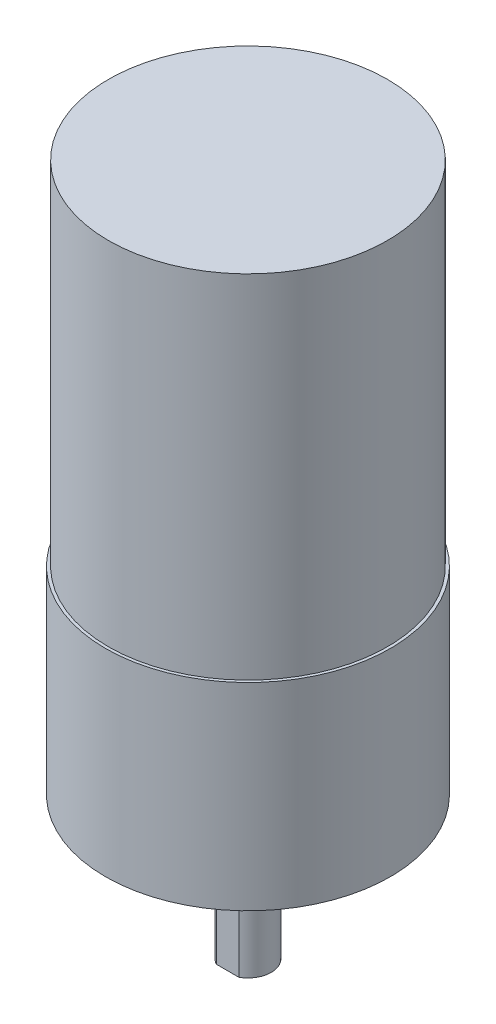
SolidWorks part; units mm, degrees
ref_plane "Front Plane" through (0, 0, 0) normal (0, 0, 1) x (1, 0, 0)
ref_plane "Top Plane" through (0, 0, 0) normal (0, 1, 0) x (1, 0, 0)
ref_plane "Right Plane" through (0, 0, 0) normal (1, 0, 0) x (0, 0, -1)
sketch "Sketch1" plane through (0, 0, 0) normal (0, 1, 0) x (1, 0, 0)
  line L0 (0, 12.446) -> (0, -12.446) construction
  line L1 (-12.446, 0) -> (12.446, 0) construction
  line L2 (-12.446, 0) -> (-9.017, 0) construction
  line L3 (9.017, 0) -> (12.446, 0) construction
  circle A0 centre (0, 0) radius 12.446
  circle A1 centre (-9.017, 0) radius 1.27
  circle A2 centre (9.017, 0) radius 1.27
  dimension "D1" = 24.892
  dimension "D3" = 2.54
  dimension "D4" = 2.54
  dimension "D2" = 18.034
extrude "Boss-Extrude1" add sketch "Sketch1" along normal blind 17.272
sketch "Sketch2" plane through (0, 17.272, 0) normal (0, 1, 0) x (1, 0, 0)
  line L0 (0, 12.446) -> (0, -12.446) construction
  line L1 (-12.446, 0) -> (12.446, 0) construction
  circle A0 centre (0, 0) radius 12.446 construction
hole_wizard "CSK for M3 Flat Head Machine Screw1" positions "Sketch3" profile "Sketch4" countersink size "M3" standard "ANSI Metric" end condition through all
sketch "Sketch3" plane through (0, 17.272, 0) normal (0, 1, 0) x (1, 0, 0)
  line L0 (0, 12.446) -> (0, -12.446) construction
  point P1 (0, 8.1199)
  point P5 (0, -7.587)
sketch "Sketch4" plane through (0, 17.272, -8.1199) normal (1, 0, 0) x (0, 0, 1)
  line L0 (0, 0) -> (0, 17.272)
  line L1 (0, 17.272) -> (1.7, 17.272)
  line L2 (1.7, 17.272) -> (1.7, 1.45)
  line L3 (1.7, 1.45) -> (3.15, 0)
  line L5 (3.15, 0) -> (0, 0)
  line L6 (-1.7, 1.45) -> (-3.15, 0) construction
  line L11 (0, -6.35) -> (0, 107.95) construction
  dimension "Thru Hole Dia." = 3.4
  dimension "Thru Hole Depth" = 17.272
  dimension "Near C'Sink Dia." = 6.3
  dimension "Near C'Sink Angle" = 90
ref_plane "Plane1" through (0, 17.272, 0) normal (0, 1, 0) x (1, 0, 0)
sketch "Sketch5" plane through (0, 17.272, 0) normal (0, 1, 0) x (1, 0, 0)
  circle A0 centre (0, 0) radius 12.192
  dimension "D1" = 24.384
extrude "Boss-Extrude2" add sketch "Sketch5" along normal blind 30.734
sketch "Sketch6" plane through (0, 0, 0) normal (0, 1, 0) x (1, 0, 0)
  circle A0 centre (0, 0) radius 3.556
  dimension "D1" = 7.112
extrude "Boss-Extrude3" add sketch "Sketch6" against normal blind 2.54
ref_plane "Plane2" through (0, -2.54, 0) normal (0, -1, 0) x (-1, 0, 0)
sketch "Sketch7" plane through (0, -2.54, 0) normal (0, -1, 0) x (-1, 0, 0)
  circle A0 centre (0, 0) radius 2.032
  dimension "D1" = 4.064
extrude "Boss-Extrude4" add sketch "Sketch7" along normal blind 9.906
ref_plane "Plane3" through (0, -12.446, 0) normal (0, -1, 0) x (-1, 0, 0)
sketch "Sketch8" plane through (0, -12.446, 0) normal (0, -1, 0) x (-1, 0, 0)
  line L0 (0, 12.446) -> (0, -12.446) construction
  line L1 (-1.016, -1.778) -> (1.016, -1.778)
  line L2 (-1.016, -1.778) -> (-1.016, -2.032)
  line L3 (-1.016, -2.032) -> (1.016, -2.032)
  line L4 (1.016, -1.778) -> (1.016, -2.032)
  line L5 (-1.016, -1.778) -> (1.016, -2.032) construction
  line L6 (-1.016, -2.032) -> (1.016, -1.778) construction
  line L7 (12.446, 0) -> (-12.446, 0) construction
  line L8 (-2.032, 0) -> (2.032, 0) construction
  line L9 (-1.016, 2.032) -> (1.016, 2.032)
  line L10 (1.016, 1.778) -> (1.016, 2.032)
  line L11 (-1.016, 1.778) -> (1.016, 1.778)
  line L12 (-1.016, 1.778) -> (-1.016, 2.032)
  circle A0 centre (0, 0) radius 2.032 construction
  point P0 (0, -1.905)
  dimension "D1" = 0.254
  dimension "D2" = 1.778
  dimension "D3" = 2.032
extrude "Cut-Extrude2" cut sketch "Sketch8" against normal blind 9.906
ref_plane "Plane4" [suppressed] through (0, 55.626, 0) normal (0, 1, 0) x (1, 0, 0)
sketch "Sketch9" [suppressed] plane through (0, 55.626, 0) normal (0, 1, 0) x (1, 0, 0)
  circle A0 centre (0, 0) radius 3.175
  dimension "D1" = 6.35
extrude "Boss-Extrude5" [suppressed] add sketch "Sketch9" along normal blind 1.524
sketch "Sketch10" [suppressed] plane through (0, 55.626, 0) normal (0, 1, 0) x (1, 0, 0)
  line L0 (0, 12.446) -> (0, -12.446) construction
  line L1 (-12.446, 0) -> (12.446, 0) construction
  line L2 (-10.033, -0.127) -> (-8.001, -0.127)
  line L3 (-10.033, -0.127) -> (-10.033, 0.127)
  line L4 (-10.033, 0.127) -> (-8.001, 0.127)
  line L5 (-8.001, -0.127) -> (-8.001, 0.127)
  line L6 (-10.033, -0.127) -> (-8.001, 0.127) construction
  line L7 (-10.033, 0.127) -> (-8.001, -0.127) construction
  line L8 (-12.192, 0) -> (-10.033, 0) construction
  line L9 (10.033, -0.127) -> (8.001, -0.127)
  line L10 (10.033, -0.127) -> (10.033, 0.127)
  line L11 (10.033, 0.127) -> (8.001, 0.127)
  line L12 (8.001, -0.127) -> (8.001, 0.127)
  line L13 (10.033, -0.127) -> (8.001, 0.127) construction
  line L14 (10.033, 0.127) -> (8.001, -0.127) construction
  line L15 (10.033, 0) -> (12.192, 0) construction
  circle A0 centre (0, 0) radius 12.192 construction
  point P4 (-9.017, 0)
  point P11 (9.017, 0)
  dimension "D1" = 18.034
  dimension "D2" = 2.032
  dimension "D3" = 0.254
  dimension "D4" = 2.032
  dimension "D5" = 0.254
extrude "Boss-Extrude6" [suppressed] add sketch "Sketch10" along normal blind 4.318
ref_plane "Plane5" [suppressed] through (0, 57.15, 0) normal (0, 1, 0) x (1, 0, 0)
sketch "Sketch11" [suppressed] plane through (0, 57.15, 0) normal (0, 1, 0) x (1, 0, 0)
  line L1 (-10.033, -0.127) -> (-8.001, -0.127)
  line L2 (-10.033, -0.127) -> (-10.033, 0.127)
  line L3 (-10.033, 0.127) -> (-8.001, 0.127)
  line L4 (-8.001, -0.127) -> (-8.001, 0.127)
  line L5 (8.001, -0.127) -> (10.033, -0.127)
  line L6 (8.001, -0.127) -> (8.001, 0.127)
  line L7 (8.001, 0.127) -> (10.033, 0.127)
  line L8 (10.033, -0.127) -> (10.033, 0.127)
  circle A0 centre (0, 0) radius 11.557
  dimension "D1" = 23.114
extrude "Boss-Extrude7" [suppressed] add sketch "Sketch11" along normal blind 0.508
ref_plane "Plane6" [suppressed] through (0, 57.658, 0) normal (0, 1, 0) x (1, 0, 0)
sketch "Sketch12" [suppressed] plane through (0, 57.658, 0) normal (0, 1, 0) x (1, 0, 0)
  line L0 (0, 12.446) -> (0, -12.446) construction
  line L1 (6.35, 3.81) -> (-6.35, 3.81)
  line L2 (6.35, 3.81) -> (6.35, 8.89)
  line L3 (6.35, 8.89) -> (-6.35, 8.89)
  line L4 (-6.35, 3.81) -> (-6.35, 8.89)
  line L5 (6.35, 3.81) -> (-6.35, 8.89) construction
  line L6 (6.35, 8.89) -> (-6.35, 3.81) construction
  point P0 (0, 6.35)
  dimension "D1" = 6.35
  dimension "D2" = 5.08
  dimension "D3" = 12.7
extrude "Boss-Extrude8" [suppressed] add sketch "Sketch12" along normal blind 2.54
sketch "Sketch13" [suppressed] plane through (0, 57.658, 0) normal (0, 1, 0) x (1, 0, 0)
  line L1 (1.905, -1.27) -> (-1.905, -1.27)
  line L2 (1.905, -1.27) -> (1.905, 1.27)
  line L3 (1.905, 1.27) -> (-1.905, 1.27)
  line L4 (-1.905, -1.27) -> (-1.905, 1.27)
  line L5 (1.905, -1.27) -> (-1.905, 1.27) construction
  line L6 (1.905, 1.27) -> (-1.905, -1.27) construction
  point P0 (0, 0)
  point P6 (-1.905, 0)
  dimension "D1" = 3.81
  dimension "D2" = 2.54
extrude "Boss-Extrude9" [suppressed] add sketch "Sketch13" along normal blind 2.794
sketch "Sketch14" [suppressed] plane through (0, 57.658, 0) normal (0, 1, 0) x (1, 0, 0)
  line L0 (-5.7185, -10.0431) -> (5.5974, -10.1111)
  line L1 (-5.7185, -10.0431) -> (-5.7005, -7.0428)
  line L2 (5.5974, -10.1111) -> (5.6154, -7.1108)
  line L3 (-5.7005, -7.0428) -> (5.6154, -7.1108)
  circle A0 centre (0, 0) radius 11.557 construction
  dimension "D1" = 11.3159
  dimension "D2" = 3.0003
  dimension "D3" = 2.3685
extrude "Boss-Extrude10" [suppressed] add sketch "Sketch14" along normal blind 9.652
ref_plane "Plane7" [suppressed] through (0, 60.452, 0) normal (0, 1, 0) x (1, 0, 0)
sketch "Sketch15" [suppressed] plane through (0, 60.452, 0) normal (0, 1, 0) x (1, 0, 0)
  circle A0 centre (0, 0) radius 3.175
  dimension "D1" = 6.35
extrude "Boss-Extrude11" [suppressed] add sketch "Sketch15" along normal blind 0.508
ref_plane "Plane8" [suppressed] through (0, 60.96, 0) normal (0, 1, 0) x (1, 0, 0)
sketch "Sketch16" [suppressed] plane through (0, 60.96, 0) normal (0, 1, 0) x (1, 0, 0)
  circle A0 centre (0, 0) radius 6.985
  dimension "D1" = 13.97
extrude "Boss-Extrude12" [suppressed] add sketch "Sketch16" along normal blind 5.842
ref_plane "Plane9" [suppressed] through (0, 67.31, 0) normal (0, 1, 0) x (1, 0, 0)
sketch "Sketch18" [suppressed] plane through (0, 67.31, 0) normal (0, 1, 0) x (1, 0, 0)
  line L0 (-5.7185, -10.0431) -> (5.5974, -10.1111)
  line L1 (-5.7185, -10.0431) -> (-5.7122, -9.0021)
  line L2 (5.5974, -10.1111) -> (5.6037, -9.07)
  line L3 (-5.7122, -9.0021) -> (5.6037, -9.07)
extrude "Cut-Extrude3" [suppressed] cut sketch "Sketch18" against normal blind 6.35
sketch "Sketch19" [suppressed] plane through (0, 66.802, 0) normal (0, 1, 0) x (1, 0, 0)
  circle A0 centre (0, 0) radius 5.08
  dimension "D1" = 10.16
extrude "Boss-Extrude13" [suppressed] add sketch "Sketch19" along normal blind 0.508
ref_plane "Plane10" [suppressed] through (0, 0, -8.89) normal (0, 0, -1) x (-1, 0, 0)
sketch "Sketch20" [suppressed] plane through (0, 0, -8.89) normal (0, 0, -1) x (-1, 0, 0)
  line L0 (0, 60.198) -> (0, 57.658) construction
  line L1 (-6.35, 60.198) -> (6.35, 60.198) construction
  line L2 (11.557, 57.658) -> (-11.557, 57.658) construction
  line L3 (-6.35, 58.928) -> (6.35, 58.928) construction
  line L4 (-6.35, 60.198) -> (-6.35, 57.658) construction
  line L5 (6.35, 60.198) -> (6.35, 57.658) construction
  circle A0 centre (-5.1435, 58.928) radius 0.9525
  circle A1 centre (-3.0861, 58.928) radius 0.9525
  circle A2 centre (-1.0287, 58.928) radius 0.9525
  circle A3 centre (1.0287, 58.928) radius 0.9525
  circle A4 centre (3.0861, 58.928) radius 0.9525
  circle A5 centre (5.1435, 58.928) radius 0.9525
  dimension "D1" = 1.905
  dimension "D2" = 1.905
  dimension "D3" = 1.905
  dimension "D4" = 1.2065
  dimension "D5" = 2.0574
  dimension "D6" = 2.0574
extrude "Boss-Extrude14" [suppressed] add sketch "Sketch20" along normal blind 12.7
equation "\"big diameter\" = .98in"
equation "\"screw distance\"= 0.71in"
equation "\"small cross holes\"= 0.10in"
